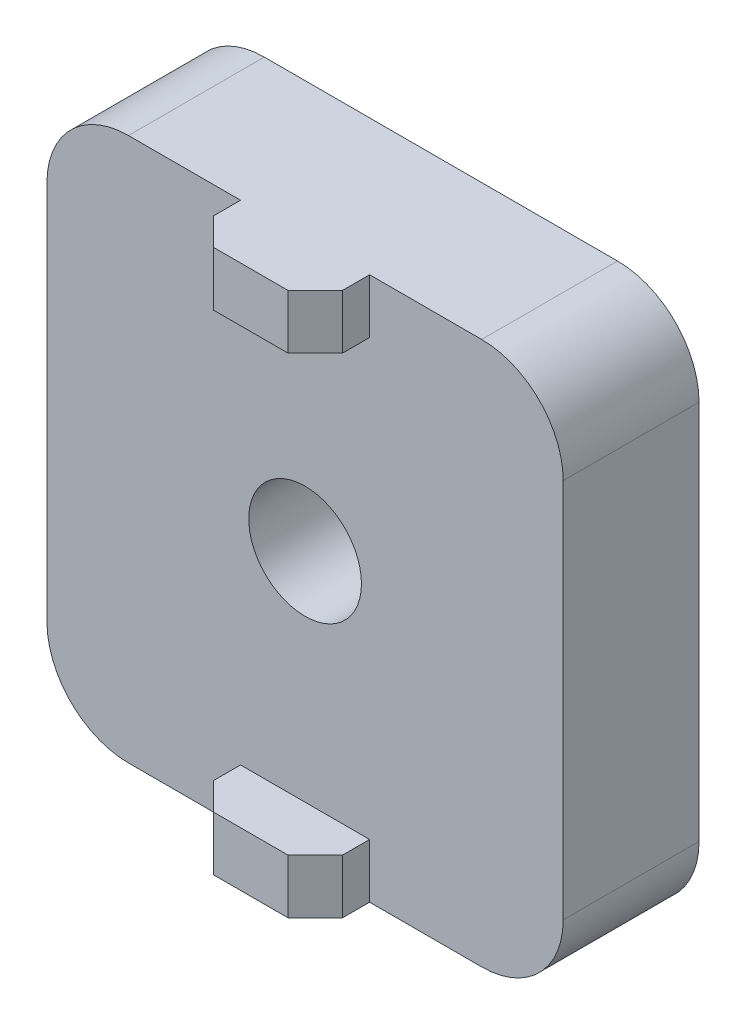
SolidWorks part; units mm, degrees
material "PET"
ref_plane "Front Plane" through (0, 0, 0) normal (0, 0, 1) x (1, 0, 0)
ref_plane "Top Plane" through (0, 0, 0) normal (0, 1, 0) x (1, 0, 0)
ref_plane "Right Plane" through (0, 0, 0) normal (1, 0, 0) x (0, 0, -1)
sketch "Sketch1" plane through (0, 0, 0) normal (0, 0, 1) x (1, 0, 0)
  line L1 (-19, -20) -> (19, -20)
  line L2 (-19, -20) -> (-19, 20)
  line L3 (-19, 20) -> (19, 20)
  line L4 (19, -20) -> (19, 20)
  line L5 (-19, -20) -> (19, 20) construction
  line L6 (-19, 20) -> (19, -20) construction
  circle A0 centre (0, 0) radius 4.15
  point P0 (0, 0)
  dimension "D2" = 8.3
  dimension "D1" = 38
  dimension "D3" = 40
extrude "Boss-Extrude1" add sketch "Sketch1" along normal mid plane 10
fillet "Fillet1" radius 6 4 edges at (-19, 20, 0) (-19, -20, 0) (19, -20, 0) (19, 20, 0)
sketch "Sketch2" plane through (0, 0, 5) normal (0, 0, 1) x (1, 0, 0)
  line L0 (13, 20) -> (-13, 20) construction
  line L1 (-4.75, 16) -> (4.75, 16)
  line L2 (-4.75, 16) -> (-4.75, 20)
  line L3 (-4.75, 20) -> (4.75, 20)
  line L4 (4.75, 16) -> (4.75, 20)
  line L5 (-4.75, 16) -> (4.75, 20) construction
  line L6 (-4.75, 20) -> (4.75, 16) construction
  line L7 (55, 0) -> (-55, 0) construction
  line L8 (4.75, -16) -> (4.75, -20)
  line L9 (-4.75, -16) -> (4.75, -16)
  line L10 (-4.75, -16) -> (4.75, -20) construction
  line L11 (-4.75, -20) -> (4.75, -20)
  line L12 (-4.75, -20) -> (4.75, -16) construction
  line L13 (-4.75, -16) -> (-4.75, -20)
  point P0 (0, 18)
  point P13 (0, -18)
  dimension "D1" = 9.5
  dimension "D2" = 4
extrude "Boss-Extrude2" add sketch "Sketch2" along normal blind 4
chamfer "Chamfer1" distance 2 angle 45 4 edges at (-4.75, -18, 9) (4.75, -18, 9) (4.75, 18, 9) (-4.75, 18, 9)
